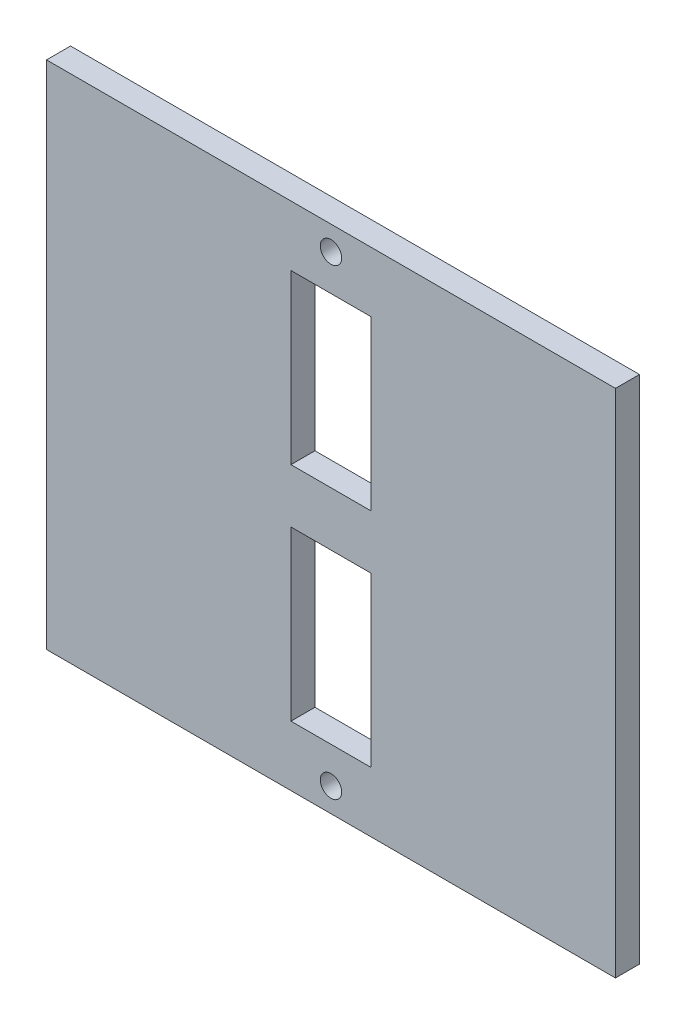
SolidWorks part; units mm, degrees
material "Maple"
ref_plane "Front Plane" through (0, 0, 0) normal (0, 0, 1) x (1, 0, 0)
ref_plane "Top Plane" through (0, 0, 0) normal (0, 1, 0) x (1, 0, 0)
ref_plane "Right Plane" through (0, 0, 0) normal (1, 0, 0) x (0, 0, -1)
sketch "Sketch1" plane through (0, 0, 0) normal (0, 0, 1) x (1, 0, 0)
  line L0 (0, 0) -> (0, 33.735) construction
  line L1 (-37.585, 33.735) -> (37.585, 33.735)
  line L2 (-37.585, 33.735) -> (-37.585, -33.735)
  line L3 (-37.585, -33.735) -> (37.585, -33.735)
  line L4 (37.585, 33.735) -> (37.585, -33.735)
  line L5 (-37.585, 33.735) -> (37.585, -33.735) construction
  line L6 (-37.585, -33.735) -> (37.585, 33.735) construction
  line L7 (0, 0) -> (12.3244, 0) construction
  line L8 (-5.29, 3.5658) -> (5.29, 3.5658)
  line L9 (-5.29, 3.5658) -> (-5.29, 25.7842)
  line L10 (-5.29, 25.7842) -> (5.29, 25.7842)
  line L11 (5.29, 3.5658) -> (5.29, 25.7842)
  line L12 (-5.29, 3.5658) -> (5.29, 25.7842) construction
  line L13 (-5.29, 25.7842) -> (5.29, 3.5658) construction
  line L14 (-5.29, -25.7842) -> (5.29, -25.7842)
  line L15 (5.29, -3.5658) -> (5.29, -25.7842)
  line L16 (-5.29, -3.5658) -> (5.29, -3.5658)
  line L17 (-5.29, -3.5658) -> (-5.29, -25.7842)
  point P0 (0, 0)
  point P8 (0, 3.55)
  point P9 (0, 25.63)
  point P10 (0, 14.675)
  point P11 (0, 14.675)
  dimension "D1" = 75.17
  dimension "D2" = 67.47
  dimension "D3" = 3.55
  dimension "D4" = 22.08
  dimension "D5" = 11.125
  dimension "D6" = 10.58
extrude "Boss-Extrude1" add sketch "Sketch1" along normal blind 3.175
sketch "Sketch2" plane through (0, 0, 3.175) normal (0, 0, 1) x (1, 0, 0)
  line L0 (-37.585, 33.735) -> (-34.403, 30.553) construction
  line L1 (-37.585, 33.735) -> (-37.585, -33.735) construction
  line L2 (0, 25.7842) -> (0, 20.5734) construction
  line L3 (5.29, 25.7842) -> (-5.29, 25.7842) construction
  line L4 (-34.403, 30.553) -> (0, 30.553) construction
  line L5 (0, 0) -> (-9.7514, 0) construction
  line L6 (0, 30.553) -> (0, 25.7842) construction
  circle A0 centre (-34.403, 30.553) radius 1.415 construction
  circle A1 centre (0, 30.553) radius 1.415
  circle A2 centre (0, -30.553) radius 1.415
  dimension "D3" = 2.83
  dimension "D4" = 2.83
  dimension "D1" = 45
  dimension "D2" = 4.5
extrude "Cut-Extrude1" cut sketch "Sketch2" against normal blind 10
equation "\"length\"= 75"
equation "\"width\"= 80mm"
equation "\"depth\"= 6.35"
equation "\"kerf\"= 0.17 / 2"
equation "\"D2@Sketch1\"= 67.30mm + 2*\"kerf\""
equation "\"D1@Sketch1\"= 75.00mm + 2*\"kerf\""
equation "\"D4@Sketch1\"= 22.25mm - 2*\"kerf\""
equation "\"D6@Sketch1\"= 10.75mm - 2*\"kerf\""
equation "\"D4@Sketch2\"= 3.00mm - 2*\"kerf\""
equation "\"D3@Sketch2\"= 3.00mm - 2*\"kerf\""
